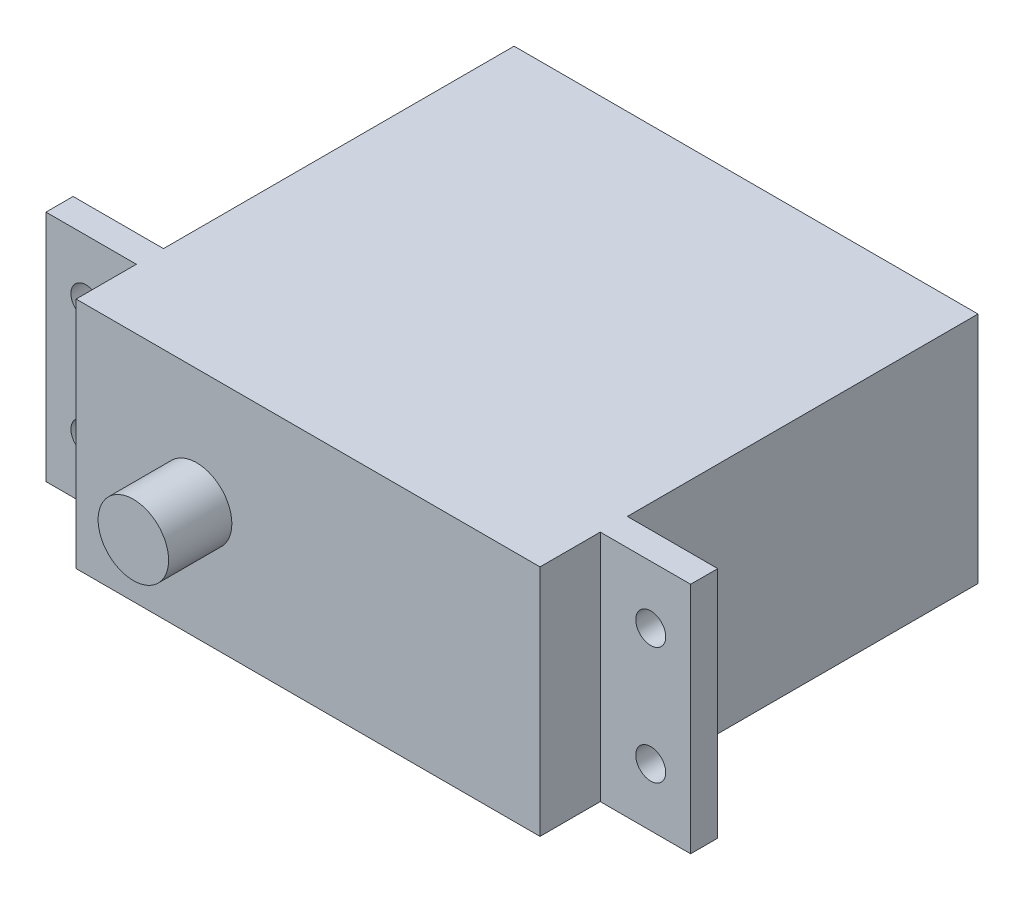
SolidWorks part; units mm, degrees
ref_plane "Front Plane" through (0, 0, 0) normal (0, 0, 1) x (1, 0, 0)
ref_plane "Top Plane" through (0, 0, 0) normal (0, 1, 0) x (1, 0, 0)
ref_plane "Right Plane" through (0, 0, 0) normal (1, 0, 0) x (0, 0, -1)
sketch "Sketch1" plane through (0, 0, 0) normal (0, 0, 1) x (1, 0, 0)
  line L0 (-27.178, -9.8425) -> (27.178, -9.8425)
  line L1 (-27.178, -9.8425) -> (-27.178, 9.8425)
  line L2 (27.178, -9.8425) -> (27.178, 9.8425)
  line L3 (-27.178, 9.8425) -> (27.178, 9.8425)
  line L4 (-27.178, -9.8425) -> (27.178, 9.8425) construction
  line L5 (27.178, -9.8425) -> (-27.178, 9.8425) construction
  point P1 (0, 0)
extrude "Extrude1" add sketch "Sketch1" along normal blind 42.2656
sketch "Sketch3" plane through (0, 0, 42.2656) normal (0, 0, 1) x (1, 0, 0)
  line L0 (-27.178, 0) -> (-9.398, 0) construction
  line L1 (-27.178, 9.8425) -> (-27.178, -9.8425) construction
  circle A0 centre (-9.398, 0) radius 2.9718
extrude "Extrude2" cut sketch "Sketch3" against normal blind 5.334 flip side to cut
sketch "Sketch7" plane through (0, 0, 42.2656) normal (0, 0, 1) x (1, 0, 0)
  line L0 (-27.178, 0) -> (-19.558, 0) construction
  line L1 (-27.178, 9.8425) -> (-27.178, -9.8425) construction
  line L2 (27.178, 0) -> (19.558, 0) construction
  line L3 (27.178, -9.8425) -> (27.178, 9.8425) construction
  line L4 (19.558, -10.1679) -> (27.178, -10.1679)
  line L5 (19.558, -10.1679) -> (19.558, 10.1679)
  line L6 (27.178, -10.1679) -> (27.178, 10.1679)
  line L7 (19.558, 10.1679) -> (27.178, 10.1679)
  line L8 (19.558, -10.1679) -> (27.178, 10.1679) construction
  line L9 (27.178, -10.1679) -> (19.558, 10.1679) construction
  line L10 (-19.558, -9.9597) -> (-27.178, -9.9597)
  line L11 (-19.558, -9.9597) -> (-19.558, 9.9597)
  line L12 (-27.178, -9.9597) -> (-27.178, 9.9597)
  line L13 (-19.558, 9.9597) -> (-27.178, 9.9597)
  line L14 (-19.558, -9.9597) -> (-27.178, 9.9597) construction
  line L15 (-27.178, -9.9597) -> (-19.558, 9.9597) construction
  point P10 (23.368, 0)
  point P11 (-23.368, 0)
extrude "Extrude4" cut sketch "Sketch7" against normal blind 10.414
sketch "Sketch8" plane through (0, 0, 0) normal (0, 0, -1) x (-1, 0, 0)
  line L0 (27.178, 0) -> (19.558, 0) construction
  line L1 (27.178, 9.8425) -> (27.178, -9.8425) construction
  line L2 (-27.178, 0) -> (-19.558, 0) construction
  line L3 (-27.178, -9.8425) -> (-27.178, 9.8425) construction
  line L4 (19.558, 9.8965) -> (27.178, 9.8965)
  line L5 (19.558, 9.8965) -> (19.558, -9.8965)
  line L6 (27.178, 9.8965) -> (27.178, -9.8965)
  line L7 (19.558, -9.8965) -> (27.178, -9.8965)
  line L8 (19.558, 9.8965) -> (27.178, -9.8965) construction
  line L9 (27.178, 9.8965) -> (19.558, -9.8965) construction
  line L10 (-19.558, 9.9934) -> (-27.178, 9.9934)
  line L11 (-19.558, 9.9934) -> (-19.558, -9.9934)
  line L12 (-27.178, 9.9934) -> (-27.178, -9.9934)
  line L13 (-19.558, -9.9934) -> (-27.178, -9.9934)
  line L14 (-19.558, 9.9934) -> (-27.178, -9.9934) construction
  line L15 (-27.178, 9.9934) -> (-19.558, -9.9934) construction
  point P10 (23.368, 0)
  point P11 (-23.368, 0)
extrude "Extrude5" cut sketch "Sketch8" against normal blind 29.5656
sketch "Sketch9" plane through (0, 0, 31.8516) normal (0, 0, 1) x (1, 0, 0)
  line L0 (23.8125, -4.953) -> (-23.8125, -4.953)
  line L1 (23.8125, -4.953) -> (23.8125, 4.953)
  line L2 (-23.8125, -4.953) -> (-23.8125, 4.953)
  line L3 (23.8125, 4.953) -> (-23.8125, 4.953)
  line L4 (23.8125, -4.953) -> (-23.8125, 4.953) construction
  line L5 (-23.8125, -4.953) -> (23.8125, 4.953) construction
  point P1 (0, 0)
hole_wizard "#39 (0.0995) Diameter Hole1" positions "3DSketch1" profile "Sketch10" hole size "#39" standard "Ansi Inch"
sketch3d "3DSketch1"
  point P0 (-23.8125, 4.953, 31.8516)
  point P3 (-23.8125, -4.953, 31.8516)
  point P6 (23.8125, 4.953, 31.8516)
  point P9 (23.8125, -4.953, 31.8516)
sketch "Sketch10" plane through (-23.8125, 4.953, 31.8516) normal (1, 0, 0) x (0, -1, 0)
  line L0 (0, 0) -> (0, 13.4593)
  line L1 (0, 13.4593) -> (1.2636, 12.7)
  line L2 (1.2636, 12.7) -> (1.2636, 0)
  line L5 (1.2636, 0) -> (0, 0)
  line L10 (0, 13.4593) -> (-1.2636, 12.7) construction
  line L11 (0, -6.35) -> (0, 107.95) construction
  dimension "Hole Dia." = 2.5273
  dimension "Hole Depth" = 12.7
  dimension "Drill Angle" = 118
